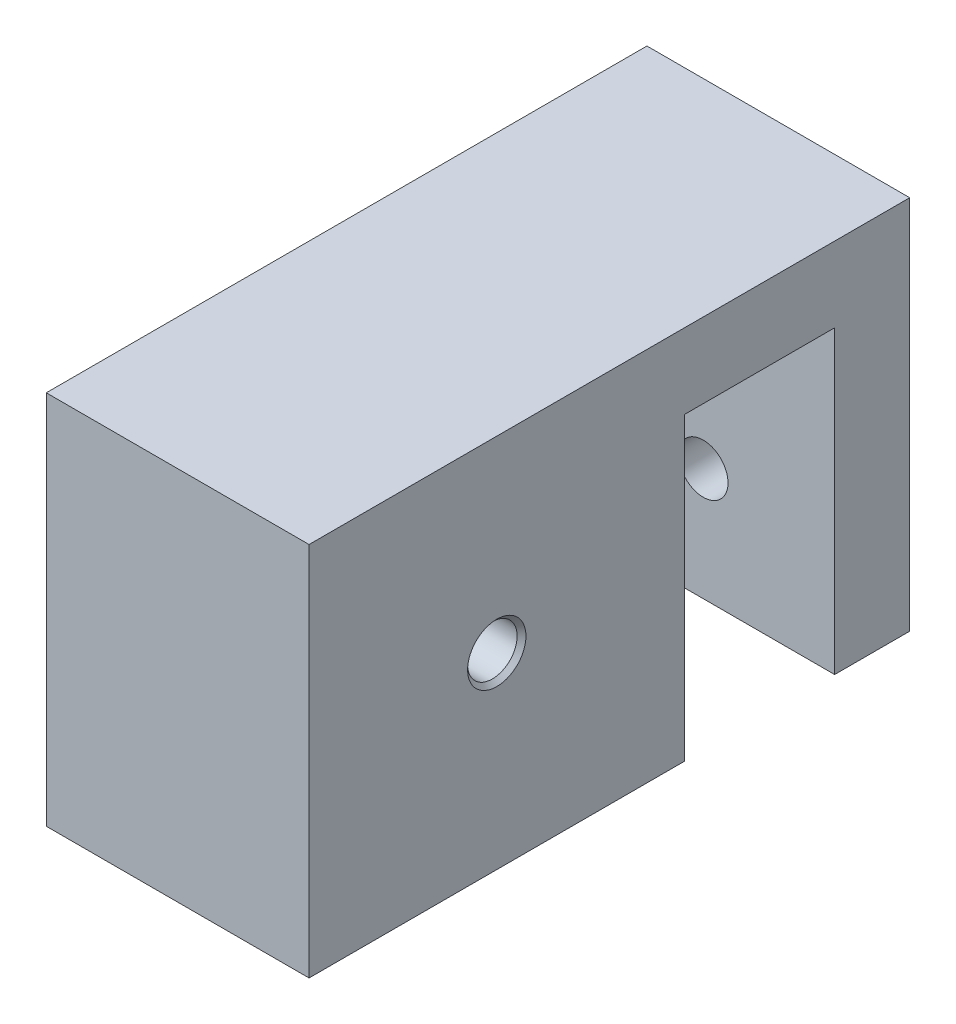
SolidWorks part; units mm, degrees
ref_plane "前视基准面" through (0, 0, 0) normal (0, 0, 1) x (1, 0, 0)
ref_plane "上视基准面" through (0, 0, 0) normal (0, 1, 0) x (1, 0, 0)
ref_plane "右视基准面" through (0, 0, 0) normal (1, 0, 0) x (0, 0, -1)
sketch "草图2" plane through (0, 0, 0) normal (1, 0, 0) x (0, 0, -1)
  line L1 (0, 0) -> (50, 0)
  line L2 (0, 0) -> (0, -50)
  line L3 (0, -50) -> (50, -50)
  line L4 (50, 0) -> (50, -50)
extrude "凸台-拉伸1" add sketch "草图2" along normal blind 35
sketch "草图3" plane through (0, 0, 0) normal (-1, 0, 0) x (0, 0, 1)
  circle A0 centre (-25, -25) radius 20
extrude "切除-拉伸1" cut sketch "草图3" against normal blind 20
hole_wizard "G1/16 螺纹孔1" positions "草图4" profile "草图5" tap size "G1/16" standard "GB"
sketch "草图4" plane through (35, 0, 0) normal (1, 0, 0) x (0, 0, -1)
  point P0 (25, -25)
sketch "草图5" plane through (35, -25, -25) normal (0, 1, 0) x (0, 0, -1)
  line L0 (0, 0) -> (0, 21.9828)
  line L1 (0, 21.9828) -> (3.3, 20)
  line L2 (3.3, 20) -> (3.3, 0.5865)
  line L3 (3.3, 0.5865) -> (3.8865, 0)
  line L5 (3.8865, 0) -> (0, 0)
  line L6 (-3.3, 0.5865) -> (-3.8865, 0) construction
  line L10 (0, 21.9828) -> (-3.3, 20) construction
  line L11 (0, -6.35) -> (0, 107.95) construction
  dimension "螺纹孔钻头直径" = 6.6
  dimension "螺纹孔钻头深度" = 20
  dimension "近端锥形沉头孔直径" = 7.773
  dimension "近端锥形沉头孔角度" = 90
  dimension "导头角度" = 118
cosmetic thread "孔螺蚊线1" parameters "D1"=15.45, "D2"=7.723
sketch "草图6" plane through (0, 0, -50) normal (0, 0, -1) x (-1, 0, 0)
  line L0 (0, -50) -> (0, 0) construction
  line L1 (-35, 0) -> (0, 0)
  line L2 (-35, 0) -> (-35, -10)
  line L3 (-35, -10) -> (0, -10)
  line L4 (0, 0) -> (0, -10)
extrude "凸台-拉伸2" add sketch "草图6" along normal blind 30
sketch "草图7" plane through (0, -10, 0) normal (0, -1, 0) x (-1, 0, 0)
  line L0 (-35, 80) -> (-35, 50) construction
  line L1 (0, 80) -> (-35, 80)
  line L2 (0, 80) -> (0, 70)
  line L3 (0, 70) -> (-35, 70)
  line L4 (-35, 80) -> (-35, 70)
extrude "凸台-拉伸3" add sketch "草图7" along normal blind 40
sketch "草图14" plane through (0, 0, 0) normal (0, 0, 1) x (1, 0, 0)
  line L0 (0, 0) -> (0, -50) construction
  line L1 (35, 0) -> (0, 0)
  line L2 (35, 0) -> (35, -10)
  line L3 (35, -10) -> (0, -10)
  line L4 (0, 0) -> (0, -10)
sketch "草图15" plane through (0, 0, -80) normal (0, 0, -1) x (-1, 0, 0)
  line L0 (-17.5, -50) -> (-17.5, -35)
  line L1 (0, -50) -> (-35, -50) construction
hole_wizard "G1/16 螺纹孔2" positions "草图16" profile "草图17" tap size "G1/16" standard "GB"
sketch "草图16" plane through (0, 0, -80) normal (0, 0, -1) x (-1, 0, 0)
  point P0 (-17.5, -35)
sketch "草图17" plane through (17.5, -35, -80) normal (1, 0, 0) x (0, 1, 0)
  line L0 (0, 0) -> (0, 21.9828)
  line L1 (0, 21.9828) -> (3.3, 20)
  line L2 (3.3, 20) -> (3.3, 0.5865)
  line L3 (3.3, 0.5865) -> (3.8865, 0)
  line L5 (3.8865, 0) -> (0, 0)
  line L6 (-3.3, 0.5865) -> (-3.8865, 0) construction
  line L10 (0, 21.9828) -> (-3.3, 20) construction
  line L11 (0, -6.35) -> (0, 107.95) construction
  dimension "螺纹孔钻头直径" = 6.6
  dimension "螺纹孔钻头深度" = 20
  dimension "近端锥形沉头孔直径" = 7.773
  dimension "近端锥形沉头孔角度" = 90
  dimension "导头角度" = 118
cosmetic thread "孔螺蚊线2" parameters "D1"=15.45, "D2"=7.723
